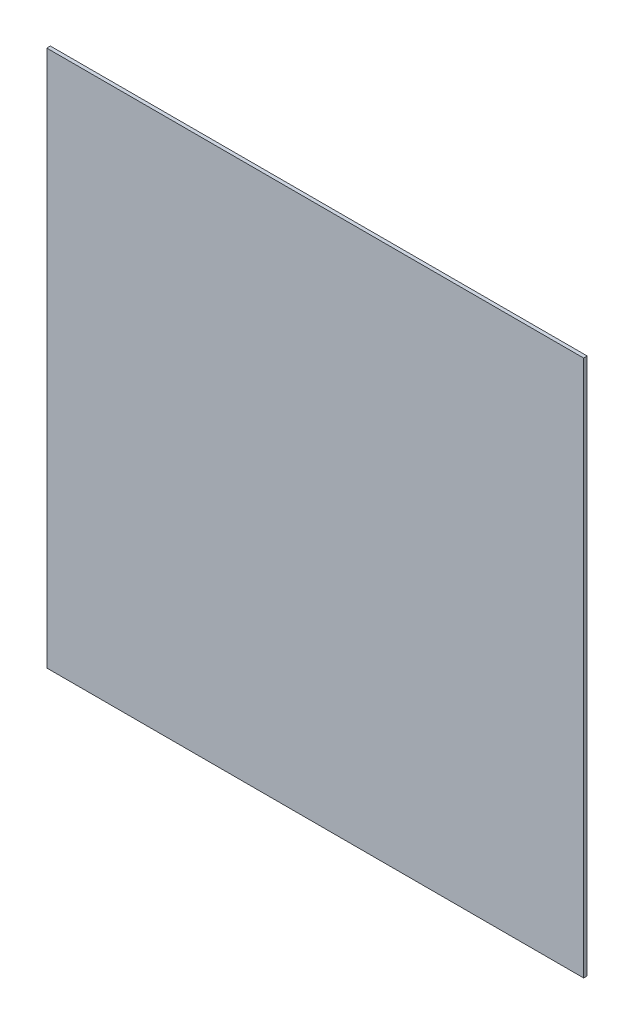
SolidWorks part; units mm, degrees
material "ABS PC"
ref_plane "Front Plane" through (0, 0, 0) normal (0, 0, 1) x (1, 0, 0)
ref_plane "Top Plane" through (0, 0, 0) normal (0, 1, 0) x (1, 0, 0)
ref_plane "Right Plane" through (0, 0, 0) normal (1, 0, 0) x (0, 0, -1)
sketch "Sketch1" plane through (0, 0, 0) normal (0, 0, 1) x (1, 0, 0)
  line L1 (-150, -150) -> (150, -150)
  line L2 (-150, -150) -> (-150, 150)
  line L3 (-150, 150) -> (150, 150)
  line L4 (150, -150) -> (150, 150)
  line L5 (-150, -150) -> (150, 150) construction
  line L6 (-150, 150) -> (150, -150) construction
  point P0 (0, 0)
  dimension "D1" = 300
  dimension "D2" = 300
extrude "Boss-Extrude1" add sketch "Sketch1" along normal blind 2
